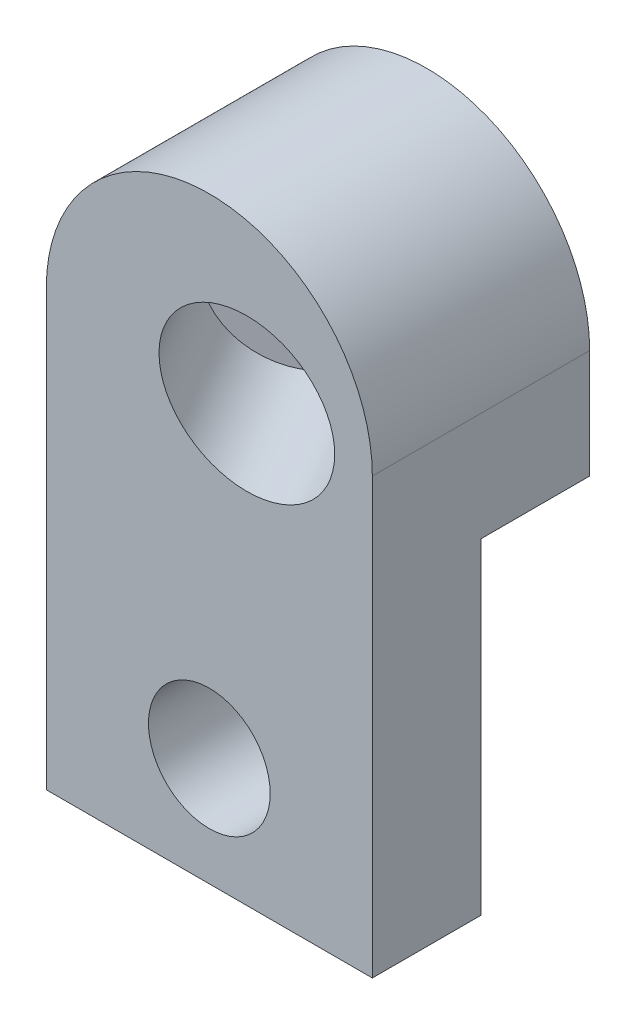
SolidWorks part; units mm, degrees
ref_plane "Front Plane" through (0, 0, 0) normal (0, 0, 1) x (1, 0, 0)
ref_plane "Top Plane" through (0, 0, 0) normal (0, 1, 0) x (1, 0, 0)
ref_plane "Right Plane" through (0, 0, 0) normal (1, 0, 0) x (0, 0, -1)
sketch "Sketch2" plane through (0, 0, 0) normal (0, 0, 1) x (1, 0, 0)
  line L0 (0, 0) -> (15, 0)
  line L1 (15, 0) -> (15, 20)
  line L2 (0, 20) -> (0, 0)
  line L3 (0, 5) -> (7.5, 5) construction
  line L4 (7.5, 5) -> (7.5, 0) construction
  line L5 (7.5, 5) -> (15, 5) construction
  arc A0 (15, 20) -> (0, 20) centre (7.5, 20) ccw
  circle A1 centre (7.5, 5) radius 2.8
  dimension "D1" = 5.6
  dimension "D3" = 20
  dimension "D2" = 15
  dimension "D4" = 5
extrude "Boss-Extrude1" add sketch "Sketch2" along normal blind 5
sketch "Sketch3" plane through (0, 0, 0) normal (0, 0, -1) x (-1, 0, 0)
  line L0 (-15, 20) -> (-15, 15)
  line L1 (-15, 0) -> (-15, 20) construction
  line L2 (-15, 15) -> (0, 15)
  line L3 (0, 20) -> (0, 0) construction
  line L4 (0, 15) -> (0, 20)
  arc A0 (0, 20) -> (-15, 20) centre (-7.5, 20) ccw
  dimension "D1" = 5
extrude "Boss-Extrude2" add sketch "Sketch3" along normal blind 5
ref_plane "Plane1" through (5.9151, 0, 10.2452) normal (0.5, 0, 0.866) x (0, 1, 0)
sketch "Sketch4" plane through (5.9151, 0, 10.2452) normal (0.5, 0, 0.866) x (0, 1, 0)
  line L2 (0, -10.4904) -> (20, -10.4904) construction
  circle A0 centre (20, -5.4904) radius 3.5
  dimension "D1" = 7
  dimension "D2" = 5
extrude "Cut-Extrude1" cut sketch "Sketch4" against normal blind 10
